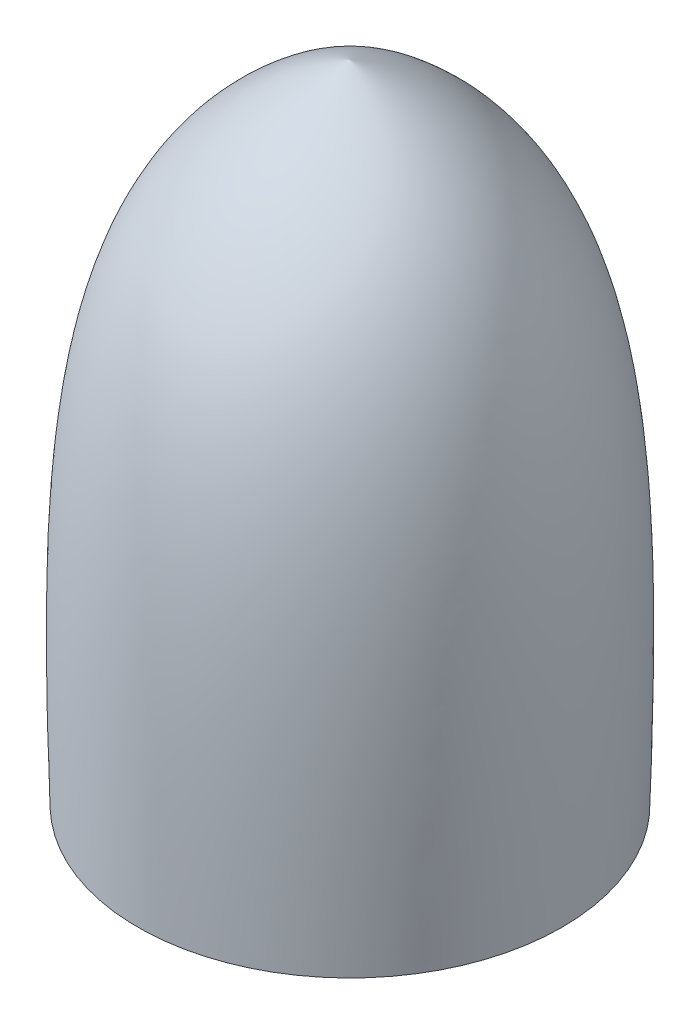
SolidWorks part; units mm, degrees
ref_plane "Front Plane" through (0, 0, 0) normal (0, 0, 1) x (1, 0, 0)
ref_plane "Top Plane" through (0, 0, 0) normal (0, 1, 0) x (1, 0, 0)
ref_plane "Right Plane" through (0, 0, 0) normal (1, 0, 0) x (0, 0, -1)
sketch "Sketch1" plane through (0, 0, 0) normal (0, 0, 1) x (1, 0, 0)
  line L0 (0, 3.696) -> (0, 2.696)
  line L1 (1.2, -3.304) -> (2.3013, -3.304)
  line L2 (1.2, -3.304) -> (1.2, 2.696)
  line L3 (1.2, 2.696) -> (0, 2.696)
  spline S0 degree 3 poles (0, 3.696) (2.3184, 2.7582) (2.4105, 0.5167) (2.3013, -3.304) knots 0 0 0 0 1 1 1 1
revolve "Revolve1" add sketch "Sketch1" angle 360 about L0
sketch "Sketch2" plane through (0, 0, 0) normal (0, 0, 1) x (1, 0, 0)
  line L0 (0.4232, 3.1837) -> (0, 3.696)
  line L1 (0, 3.696) -> (0.4232, 3.1837)
  line L2 (0, 3.696) -> (-0.4172, 3.1788)
  arc A0 (0.4232, 3.1837) -> (-0.4172, 3.1788) centre (0.005, 2.8382) ccw
